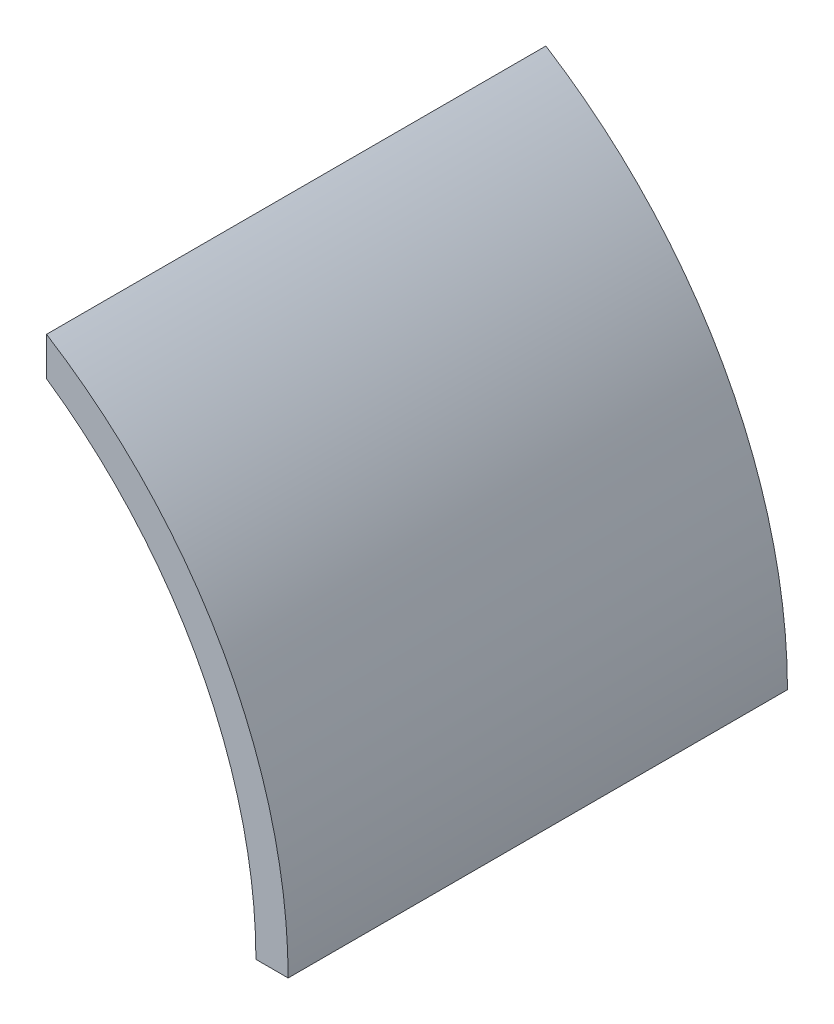
SolidWorks part; units mm, degrees
material "201 Annealed Stainless Steel (SS)"
ref_plane "Front Plane" through (0, 0, 0) normal (0, 0, 1) x (1, 0, 0)
ref_plane "Top Plane" through (0, 0, 0) normal (0, 1, 0) x (1, 0, 0)
ref_plane "Right Plane" through (0, 0, 0) normal (1, 0, 0) x (0, 0, -1)
sketch "Sketch2" plane through (0, 0, 0) normal (0, 0, 1) x (1, 0, 0)
  line L0 (-150, 0) -> (150, 0) construction
  line L1 (0, 150) -> (0, -160) construction
  line L2 (85, 0) -> (85, 108.9269) construction
  line L7 (85, 135.5544) -> (85, 123.5921)
  line L8 (0, -160) -> (0, -160.382) construction
  line L21 (150, 0) -> (160, 0)
  circle A0 centre (0, 0) radius 150 construction
  circle A1 centre (0, 0) radius 160 construction
  arc A2 (85, 123.5921) -> (150, 0) centre (0, 0) cw
  arc A3 (160, 0) -> (85, 135.5544) centre (0, 0) ccw
  dimension "D1" = 300
  dimension "D2" = 320
  dimension "D3" = 85
extrude "Inner Ring - Right Side" add sketch "Sketch2" along normal blind 155
